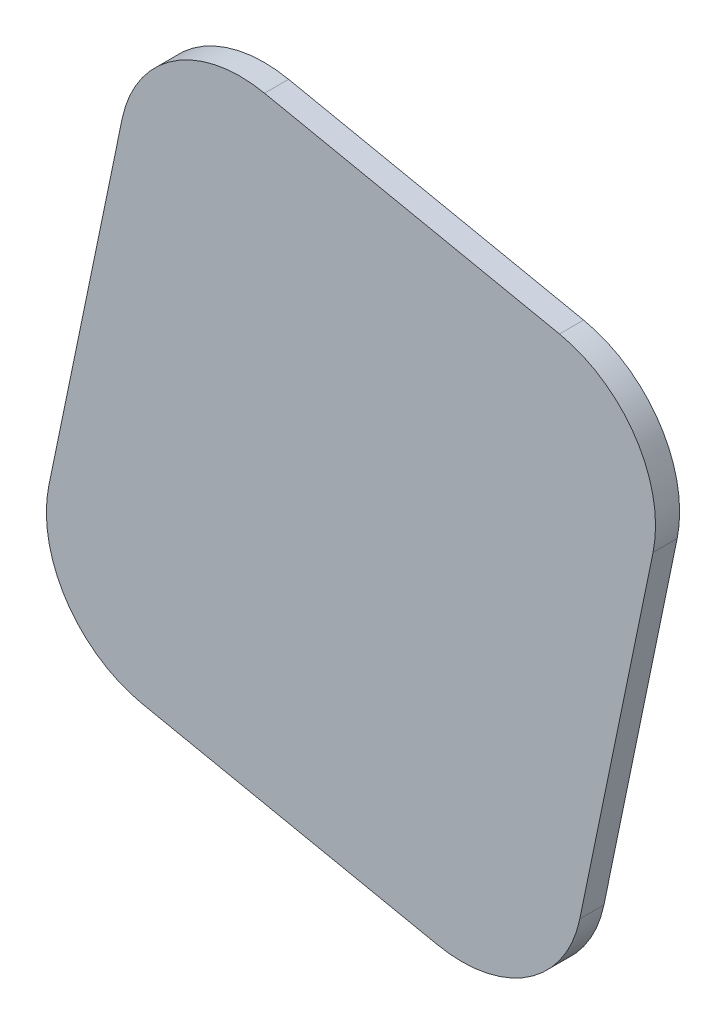
SolidWorks part; units mm, degrees
ref_plane "Plan de face" through (0, 0, 0) normal (0, 0, 1) x (1, 0, 0)
ref_plane "Plan de dessus" through (0, 0, 0) normal (0, 1, 0) x (1, 0, 0)
ref_plane "Plan de droite" through (0, 0, 0) normal (1, 0, 0) x (0, 0, -1)
sketch "Esquisse1" plane through (0, 0, 0) normal (0, 0, 1) x (1, 0, 0)
  line L0 (-99.2092, 80.7637) -> (-55.1425, 71.6464)
  line L1 (-99.2092, 80.7637) -> (-109.3395, 31.8006)
  line L2 (-55.1425, 71.6464) -> (-65.2728, 22.6834)
  line L3 (-109.3395, 31.8006) -> (-65.2728, 22.6834)
  dimension "D1" = 45
  dimension "D2" = 50
extrude "Boss.-Extru.1" add sketch "Esquisse1" along normal blind 2
fillet "Congé1" radius 10 4 edges at (-99.2092, 80.7637, 1) (-55.1425, 71.6464, 1) (-65.2728, 22.6834, 1) (-109.3395, 31.8006, 1)
